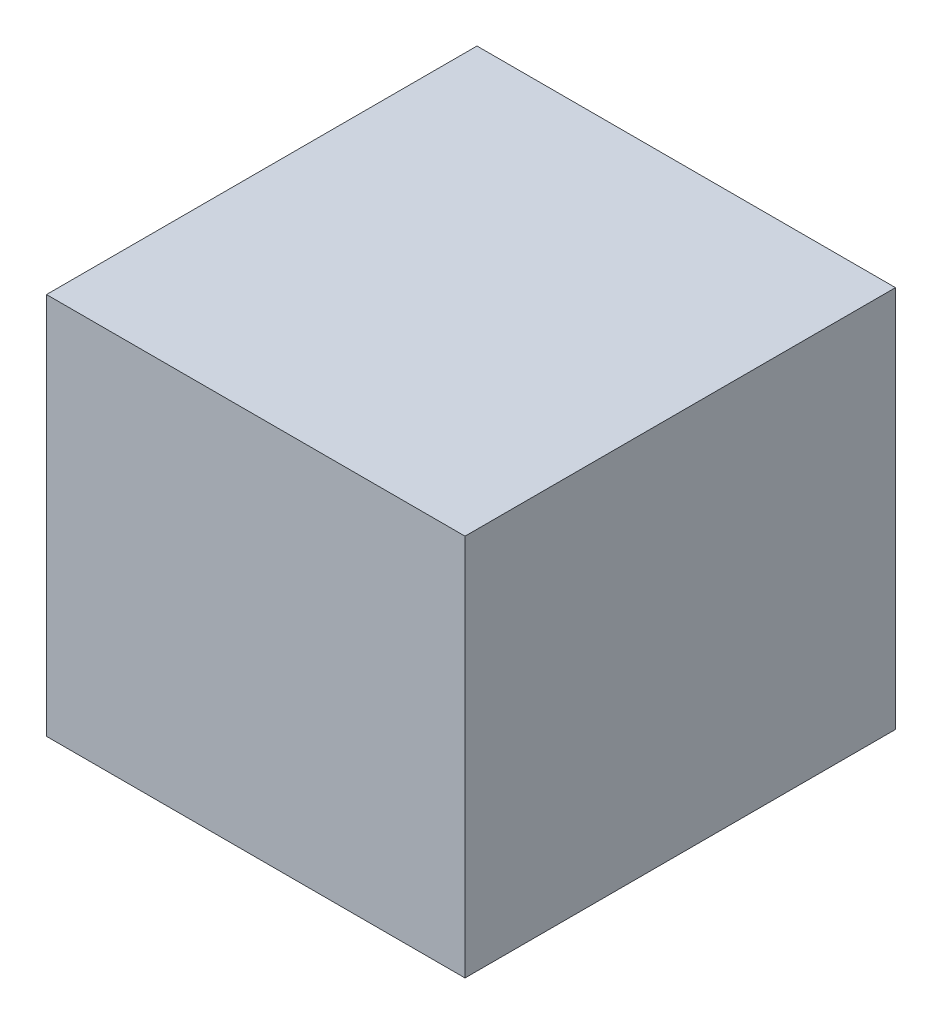
SolidWorks part; units mm, degrees
ref_plane "Piano frontale" through (0, 0, 0) normal (0, 0, 1) x (1, 0, 0)
ref_plane "Piano superiore" through (0, 0, 0) normal (0, 1, 0) x (1, 0, 0)
ref_plane "Piano destro" through (0, 0, 0) normal (1, 0, 0) x (0, 0, -1)
sketch "Schizzo1" plane through (0, 0, 0) normal (0, 0, 1) x (1, 0, 0)
  line L1 (-17.5, 13.5) -> (17.5, 13.5)
  line L2 (-17.5, 13.5) -> (-17.5, -13.5)
  line L3 (-17.5, -13.5) -> (17.5, -13.5)
  line L4 (17.5, 13.5) -> (17.5, -13.5)
  line L5 (-17.5, 13.5) -> (17.5, -13.5) construction
  line L6 (-17.5, -13.5) -> (17.5, 13.5) construction
  line L7 (-10, 10) -> (10, 10) construction
  line L8 (-10, 10) -> (-10, -10) construction
  line L9 (-10, -10) -> (10, -10) construction
  line L10 (10, 10) -> (10, -10) construction
  line L11 (-10, 10) -> (10, -10) construction
  line L12 (-10, -10) -> (10, 10) construction
  point P0 (0, 0)
  point P7 (0, 0)
  dimension "D1" = 35
  dimension "D2" = 27
  dimension "D3" = 20
  dimension "D4" = 20
extrude "Estrusione-Estrusione1" add sketch "Schizzo1" along normal blind 36
sketch "Schizzo3" plane through (0, 13.5, 0) normal (0, 1, 0) x (1, 0, 0)
  line L0 (-17.5, 0) -> (17.5, -36) construction
  line L1 (-17.5, -36) -> (17.5, 0) construction
  circle A0 centre (0, -18) radius 5
  point P10 (0, 0)
  point P11 (0, -18)
  point P12 (0, -18)
  dimension "D1" = 10
extrude "Taglio-Estrusione1" cut sketch "Schizzo3" against normal through all
sketch "Schizzo4" plane through (0, -13.5, 0) normal (0, -1, 0) x (1, 0, 0)
  circle A0 centre (0, 18) radius 11
  dimension "D1" = 22
extrude "Taglio-Estrusione2" cut sketch "Schizzo4" against normal blind 3.5
sketch "Schizzo7" plane through (0, 13.5, 0) normal (0, 1, 0) x (1, 0, 0)
  line L1 (-17.5, 0) -> (17.5, 0)
  line L2 (-17.5, 0) -> (-17.5, -36)
  line L3 (-17.5, -36) -> (17.5, -36)
  line L4 (17.5, 0) -> (17.5, -36)
  line L5 (-17.5, 0) -> (17.5, -36) construction
  line L6 (-17.5, -36) -> (17.5, 0) construction
  point P0 (0, -18)
extrude "Estrusione-Estrusione3" add sketch "Schizzo7" along normal blind 5
